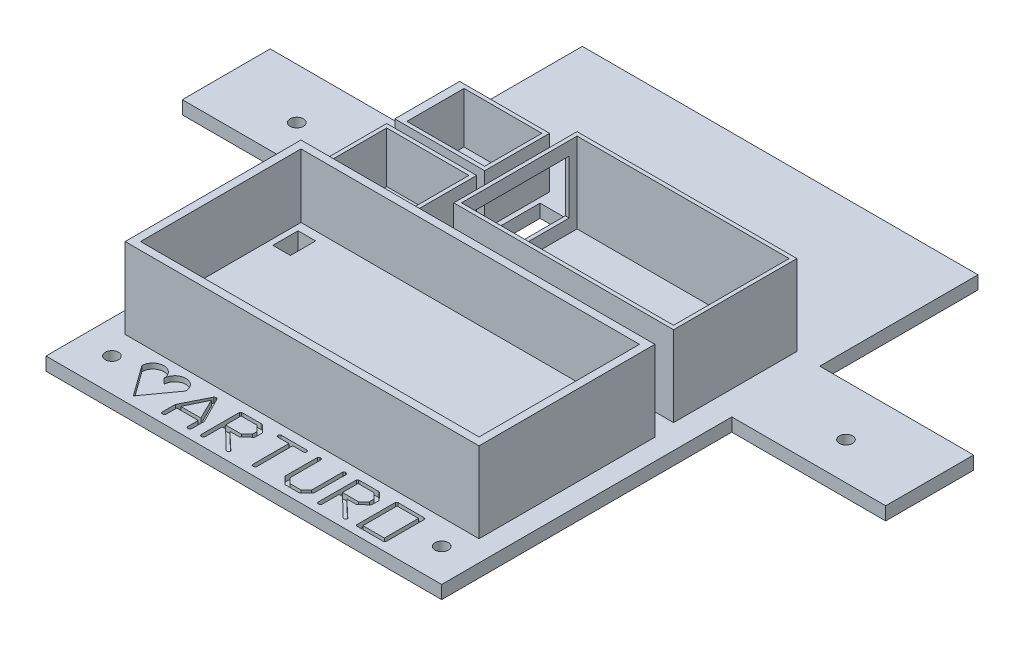
SolidWorks part; units mm, degrees
ref_plane "Front Plane" through (0, 0, 0) normal (0, 0, 1) x (1, 0, 0)
ref_plane "Top Plane" through (0, 0, 0) normal (0, 1, 0) x (1, 0, 0)
ref_plane "Right Plane" through (0, 0, 0) normal (1, 0, 0) x (0, 0, -1)
sketch "Sketch1" plane through (0, 0, 0) normal (0, 1, 0) x (1, 0, 0)
  line L1 (0, 0) -> (90, 0)
  line L2 (0, 0) -> (0, 145)
  line L3 (0, 145) -> (90, 145)
  line L4 (90, 0) -> (90, 145)
  dimension "D1" = 145
  dimension "D2" = 90
extrude "Boss-Extrude1" add sketch "Sketch1" along normal blind 3 contours L2 L3 L4 L1
sketch "Sketch3" plane through (0, 3, 0) normal (0, 1, 0) x (1, 0, 0)
  line L0 (90, 0) -> (90, 145) construction
  line L1 (90, 86) -> (125, 86)
  line L2 (90, 86) -> (90, 66)
  line L3 (90, 66) -> (125, 66)
  line L4 (125, 86) -> (125, 66)
  line L5 (0, 0) -> (90, 0) construction
  line L6 (0, 0) -> (0, 145) construction
  line L7 (0, 86) -> (-35, 86)
  line L8 (0, 86) -> (0, 66)
  line L9 (0, 66) -> (-35, 66)
  line L10 (-35, 86) -> (-35, 66)
  dimension "D1" = 66
extrude "Boss-Extrude2" add sketch "Sketch3" against normal blind 3
sketch "Sketch2" plane through (0, 3, 0) normal (0, 1, 0) x (1, 0, 0)
  circle A0 centre (7.5, 7.5) radius 1.5
  circle A1 centre (82.5, 7.5) radius 1.5
  dimension "D3" = 3
extrude "Cut-Extrude1" cut sketch "Sketch2" against normal blind 3
sketch "Sketch5" plane through (0, 3, 0) normal (0, 1, 0) x (1, 0, 0)
  line L0 (0, 0) -> (90, 0) construction
  line L1 (4.75, 53.25) -> (85.25, 53.25)
  line L2 (4.75, 53.25) -> (4.75, 13.25)
  line L3 (4.75, 13.25) -> (85.25, 13.25)
  line L4 (85.25, 53.25) -> (85.25, 13.25)
  line L5 (45, 145) -> (45, 77.1413) construction
  line L6 (0, 0) -> (0, 66) construction
  line L7 (0, 145) -> (90, 145) construction
  point P9 (4.75, 33.25)
  point P11 (45, 53.25)
  dimension "D1" = 13.25
  dimension "D2" = 0
  dimension "D3" = 40
  dimension "D4" = 80.5
  dimension "D5" = 4.75
extrude "Boss-Extrude3" add sketch "Sketch5" along normal blind 18.3
sketch "Sketch7" plane through (0, 21.3, 0) normal (0, 1, 0) x (1, 0, 0)
  line L0 (45, 13.25) -> (45, 53.25) construction
  line L5 (4.75, 13.25) -> (85.25, 13.25) construction
  line L6 (85.25, 53.25) -> (4.75, 53.25) construction
  line L8 (83.5, 15) -> (6.5, 15)
  line L9 (83.5, 15) -> (83.5, 51.5)
  line L10 (83.5, 51.5) -> (6.5, 51.5)
  line L11 (6.5, 15) -> (6.5, 51.5)
  line L12 (83.5, 15) -> (6.5, 51.5) construction
  line L13 (83.5, 51.5) -> (6.5, 15) construction
  point P6 (45, 33.25)
extrude "Cut-Extrude3" cut sketch "Sketch7" against normal blind 14.5
sketch "Sketch14" plane through (0, 6.8, 0) normal (0, 1, 0) x (1, 0, 0)
  line L1 (11.8026, 49.53) -> (7.8026, 49.53)
  line L2 (11.8026, 49.53) -> (11.8026, 43.798)
  line L3 (11.8026, 43.798) -> (7.8026, 43.798)
  line L4 (7.8026, 49.53) -> (7.8026, 43.798)
  line L5 (11.8026, 49.53) -> (7.8026, 43.798) construction
  line L6 (11.8026, 43.798) -> (7.8026, 49.53) construction
  point P0 (9.8026, 46.664)
extrude "Cut-Extrude6" cut sketch "Sketch14" against normal through all
sketch "Sketch8" plane through (0, 3, 0) normal (0, 1, 0) x (1, 0, 0)
  line L0 (4.75, 36.7092) -> (0, 36.7092) construction
  line L1 (4.5, 73) -> (24.95, 73)
  line L2 (4.5, 73) -> (4.5, 58.25)
  line L3 (4.5, 58.25) -> (24.95, 58.25)
  line L4 (24.95, 73) -> (24.95, 58.25)
  line L5 (4.75, 53.25) -> (4.75, 13.25) construction
  line L6 (85.25, 53.25) -> (4.75, 53.25) construction
  line L7 (4.5, 89.5891) -> (24.95, 89.5891)
  line L8 (4.5, 89.5891) -> (4.5, 74.8391)
  line L9 (4.5, 74.8391) -> (24.95, 74.8391)
  line L10 (24.95, 89.5891) -> (24.95, 74.8391)
  line L11 (0, 0) -> (0, 66) construction
  line L13 (0, 86) -> (0, 145) construction
  dimension "D1" = 20.45
  dimension "D2" = 5
  dimension "D3" = 14.75
  dimension "D4" = 4.5
  dimension "D5" = 4.5
extrude "Boss-Extrude4" add sketch "Sketch8" along normal blind 11.55
sketch "Sketch11" plane through (0, 14.55, 0) normal (0, 1, 0) x (1, 0, 0)
  line L1 (23.475, 69.875) -> (13.775, 69.875)
  line L2 (23.475, 69.875) -> (23.475, 61.375)
  line L3 (23.475, 61.375) -> (13.775, 61.375)
  line L5 (24.95, 58.25) -> (24.95, 73) construction
  line L6 (28.0802, 73) -> (28.0802, 58.25) construction
  line L7 (24.95, 73) -> (4.5, 73) construction
  line L8 (4.5, 58.25) -> (24.95, 58.25) construction
  line L10 (23.475, 77.9641) -> (13.775, 77.9641)
  line L11 (23.475, 77.9641) -> (23.475, 86.4641)
  line L12 (23.475, 86.4641) -> (13.775, 86.4641)
  line L14 (24.95, 89.5891) -> (4.5, 89.5891) construction
  line L15 (4.5, 74.8391) -> (24.95, 74.8391) construction
  line L16 (24.95, 74.8391) -> (24.95, 89.5891) construction
  arc A0 (13.775, 77.9641) -> (13.775, 86.4641) centre (13.775, 82.2141) cw
  arc A1 (13.775, 61.375) -> (13.775, 69.875) centre (13.775, 65.625) cw
  point P12 (28.0802, 65.625)
  point P13 (23.475, 65.625)
  dimension "D1" = 9.7
  dimension "D2" = 1.475
  dimension "D3" = 0
  dimension "D4" = 8.5
  dimension "D5" = 1.475
  dimension "D6" = 3.125
  dimension "D7" = 3.125
  dimension "D8" = 3.125
  dimension "D9" = 3.125
  dimension "D10" = 1.475
  dimension "D11" = 9.7
extrude "Cut-Extrude4" cut sketch "Sketch11" against normal through all
sketch "Sketch12" plane through (0, 14.55, 0) normal (0, 1, 0) x (1, 0, 0)
  line L1 (23.475, 69.875) -> (13.775, 69.875)
  line L2 (23.475, 69.875) -> (23.475, 61.375)
  line L3 (23.475, 61.375) -> (13.775, 61.375)
  line L4 (13.775, 69.875) -> (13.775, 61.375)
extrude "Boss-Extrude5" add sketch "Sketch12" against normal blind 11.55
sketch "Sketch13" plane through (0, 14.55, 0) normal (0, 1, 0) x (1, 0, 0)
  line L0 (24.95, 65.625) -> (4.5, 65.625) construction
  line L1 (24.95, 58.25) -> (24.95, 73) construction
  line L2 (4.5, 73) -> (4.5, 58.25) construction
  line L4 (5.375, 72.125) -> (24.075, 72.125)
  line L5 (5.375, 72.125) -> (5.375, 59.125)
  line L6 (5.375, 59.125) -> (24.075, 59.125)
  line L7 (24.075, 72.125) -> (24.075, 59.125)
  line L8 (5.375, 72.125) -> (24.075, 59.125) construction
  line L9 (5.375, 59.125) -> (24.075, 72.125) construction
  line L13 (6.375, 88.7141) -> (24.075, 88.7141)
  line L14 (6.375, 88.7141) -> (6.375, 75.7141)
  line L15 (6.375, 75.7141) -> (24.075, 75.7141)
  line L16 (24.075, 88.7141) -> (24.075, 75.7141)
  line L17 (24.95, 74.8391) -> (24.95, 89.5891) construction
  line L18 (24.95, 89.5891) -> (4.5, 89.5891) construction
  line L19 (4.5, 74.8391) -> (24.95, 74.8391) construction
  line L20 (0, 86) -> (0, 145) construction
  point P6 (14.725, 65.625)
  dimension "D1" = 0.875
  dimension "D2" = 0.875
  dimension "D3" = 0.875
  dimension "D4" = 6.375
extrude "Cut-Extrude5" cut sketch "Sketch13" against normal blind 11.55
sketch "Sketch19" plane through (0, 3, 0) normal (0, 1, 0) x (1, 0, 0)
  line L0 (85.25, 53.25) -> (4.75, 53.25) construction
  line L1 (84.5, 58.25) -> (34.5, 58.25)
  line L2 (84.5, 58.25) -> (84.5, 86.3)
  line L3 (84.5, 86.3) -> (34.5, 86.3)
  line L4 (34.5, 58.25) -> (34.5, 86.3)
  line L7 (90, 0) -> (90, 66) construction
  dimension "D1" = 28.05
  dimension "D2" = 50
  dimension "D3" = 5
  dimension "D4" = 5.5
extrude "Boss-Extrude6" add sketch "Sketch19" along normal blind 18.3
sketch "Sketch20" plane through (0, 21.3, 0) normal (0, 1, 0) x (1, 0, 0)
  line L0 (84.5, 72.275) -> (34.5, 72.275) construction
  line L1 (84.5, 58.25) -> (84.5, 86.3) construction
  line L2 (34.5, 86.3) -> (34.5, 58.25) construction
  line L4 (83.625, 85.425) -> (35.375, 85.425)
  line L5 (83.625, 85.425) -> (83.625, 59.125)
  line L6 (83.625, 59.125) -> (35.375, 59.125)
  line L7 (35.375, 85.425) -> (35.375, 59.125)
  line L8 (83.625, 85.425) -> (35.375, 59.125) construction
  line L9 (83.625, 59.125) -> (35.375, 85.425) construction
  point P6 (59.5, 72.275)
extrude "Cut-Extrude7" cut sketch "Sketch20" against normal blind 18.3
sketch "Sketch22" plane through (34.5, 0, 0) normal (-1, 0, 0) x (0, 0, 1)
  line L0 (-72.275, 21.3) -> (-72.275, 3) construction
  line L1 (-86.3, 21.3) -> (-58.25, 21.3) construction
  line L2 (-86.3, 3) -> (-58.25, 3) construction
  line L4 (-83.6319, 6.0463) -> (-60.9181, 6.0463)
  line L5 (-83.6319, 6.0463) -> (-83.6319, 18.2537)
  line L6 (-83.6319, 18.2537) -> (-60.9181, 18.2537)
  line L7 (-60.9181, 6.0463) -> (-60.9181, 18.2537)
  line L8 (-83.6319, 6.0463) -> (-60.9181, 18.2537) construction
  line L9 (-83.6319, 18.2537) -> (-60.9181, 6.0463) construction
  point P6 (-72.275, 12.15)
extrude "Cut-Extrude8" cut sketch "Sketch22" against normal blind 1.75
sketch "Sketch23" plane through (0, 3, 0) normal (0, 1, 0) x (1, 0, 0)
  line L0 (24.95, 74.8391) -> (24.95, 89.5891) construction
  line L1 (33.375, 86.3) -> (26.075, 86.3)
  line L2 (33.375, 86.3) -> (33.375, 58.3)
  line L3 (33.375, 58.3) -> (26.075, 58.3)
  line L4 (26.075, 86.3) -> (26.075, 58.3)
  line L5 (34.5, 86.3) -> (34.5, 58.25) construction
  line L6 (84.5, 86.3) -> (34.5, 86.3) construction
  line L7 (34.5, 58.25) -> (84.5, 58.25) construction
  dimension "D1" = 1.125
  dimension "D2" = 7.3
  dimension "D3" = 28
  dimension "D4" = 1.125
  dimension "D5" = 0
  dimension "D6" = 0.05
extrude "Cut-Extrude9" cut sketch "Sketch23" against normal through all
sketch "Sketch24" plane through (0, 3, 0) normal (0, 1, 0) x (1, 0, 0)
  line L0 (6.5, 51.5) -> (6.5, 15) construction
  line L2 (12.8, 9.003) -> (17.8, 2.0665)
  line L3 (17.8, 2.0665) -> (22.8, 9.003)
  line L4 (0, 0) -> (0, 66) construction
  arc A0 (17.8, 9.003) -> (12.8, 9.003) centre (15.3, 9.003) ccw
  arc A1 (22.8, 9.003) -> (17.8, 9.003) centre (20.3, 9.003) ccw
  text T0 "ARTURO" font "SWTxt" height in points 36
  dimension "D1" = 5
  dimension "D2" = 36.5
  dimension "D3" = 17.8
extrude "Cut-Extrude10" cut sketch "Sketch24" against normal blind 1.2
sketch "Sketch25" plane through (0, 3, 0) normal (0, 1, 0) x (1, 0, 0)
  circle A0 centre (-17.4688, 74.5) radius 1.5
  circle A1 centre (107.4688, 74.5) radius 1.5
extrude "Cut-Extrude11" cut sketch "Sketch25" against normal through all
sketch "Sketch26" plane through (0, 3, 0) normal (0, 1, 0) x (1, 0, 0)
  line L0 (90, 86) -> (90, 145) construction
  line L1 (0, 145) -> (90, 145)
  line L2 (0, 145) -> (0, 122)
  line L3 (0, 122) -> (90, 122)
  line L4 (90, 145) -> (90, 122)
extrude "Cut-Extrude12" cut sketch "Sketch26" against normal through all
